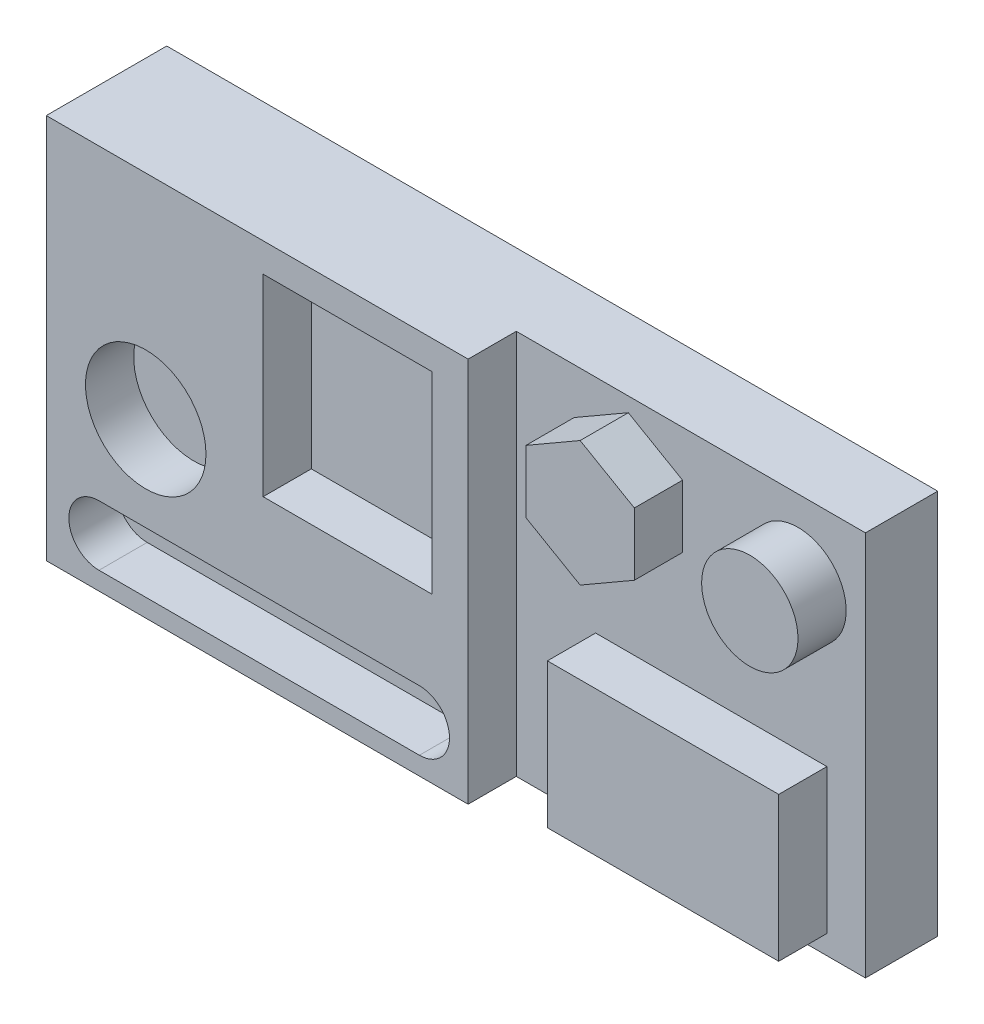
SolidWorks part; units mm, degrees
ref_plane "Front Plane" through (0, 0, 0) normal (0, 0, 1) x (1, 0, 0)
ref_plane "Top Plane" through (0, 0, 0) normal (0, 1, 0) x (1, 0, 0)
ref_plane "Right Plane" through (0, 0, 0) normal (1, 0, 0) x (0, 0, -1)
sketch "Sketch1" plane through (0, 0, 0) normal (0, 0, 1) x (1, 0, 0)
  line L0 (-87.7106, -38.1) -> (-3.262, -38.1) construction
  line L1 (-101.6, 50.8) -> (101.6, 50.8)
  line L2 (-101.6, 50.8) -> (-101.6, -50.8)
  line L3 (-101.6, -50.8) -> (101.6, -50.8)
  line L4 (101.6, 50.8) -> (101.6, -50.8)
  line L5 (-101.6, 50.8) -> (101.6, -50.8) construction
  line L6 (-101.6, -50.8) -> (101.6, 50.8) construction
  line L7 (-87.7106, -30.1625) -> (-3.262, -30.1625)
  line L8 (-87.7106, -46.0375) -> (-3.262, -46.0375)
  line L9 (9.5793, 50.8) -> (9.5793, -50.8)
  line L10 (-44.45, 43.18) -> (0, 43.18)
  line L11 (-44.45, 43.18) -> (-44.45, -7.62)
  line L12 (-44.45, -7.62) -> (0, -7.62)
  line L13 (0, 43.18) -> (0, -7.62)
  line L15 (30.48, -7.62) -> (91.44, -7.62)
  line L16 (30.48, -7.62) -> (30.48, -45.72)
  line L17 (30.48, -45.72) -> (91.44, -45.72)
  line L18 (91.44, -7.62) -> (91.44, -45.72)
  line L19 (39.1068, 13.9822) -> (53.3943, 22.2311)
  line L20 (53.3943, 22.2311) -> (53.3943, 38.7289)
  line L21 (53.3943, 38.7289) -> (39.1068, 46.9778)
  line L22 (39.1068, 46.9778) -> (24.8193, 38.7289)
  line L23 (24.8193, 38.7289) -> (24.8193, 22.2311)
  line L24 (24.8193, 22.2311) -> (39.1068, 13.9822)
  arc A0 (-87.7106, -30.1625) -> (-87.7106, -46.0375) centre (-87.7106, -38.1) ccw
  arc A1 (-3.262, -46.0375) -> (-3.262, -30.1625) centre (-3.262, -38.1) ccw
  circle A2 centre (-75.3876, -5.4366) radius 15.875
  circle A3 centre (83.82, 30.48) radius 12.7
  circle A4 centre (39.1068, 30.48) radius 14.2875 construction
  point P0 (0, 0)
  point P8 (-45.4863, -38.1)
  dimension "D5" = 31.75
  dimension "D10" = 25.4
  dimension "D1" = 101.6
  dimension "D2" = 203.2
  dimension "D3" = 15.875
  dimension "D4" = 12.7
  dimension "D6" = 57.15
  dimension "D7" = 44.45
  dimension "D8" = 7.62
  dimension "D9" = 50.8
  dimension "D11" = 60.96
  dimension "D12" = 38.1
  dimension "D13" = 5.08
  dimension "D14" = 17.78
  dimension "D15" = 20.32
  dimension "D16" = 15.24
  dimension "D17" = 28.575
sketch "Sketch2" plane through (0, 0, 0) normal (0, 0, 1) x (1, 0, 0)
  line L0 (-101.6, 50.8) -> (101.6, 50.8) construction
  line L1 (101.6, 50.8) -> (101.6, -50.8) construction
  line L2 (-101.6, -50.8) -> (101.6, -50.8) construction
  line L3 (-101.6, 50.8) -> (-101.6, -50.8) construction
  line L4 (-101.6, 50.8) -> (101.6, 50.8)
  line L5 (101.6, 50.8) -> (101.6, -50.8)
  line L6 (-101.6, -50.8) -> (101.6, -50.8)
  line L7 (-101.6, 50.8) -> (-101.6, -50.8)
extrude "Boss-Extrude1" add sketch "Sketch2" along normal blind 31.75
ref_plane "Plane1" through (0, 0, 31.75) normal (0, 0, 1) x (1, 0, 0)
sketch "Sketch3" plane through (0, 0, 31.75) normal (0, 0, 1) x (1, 0, 0)
  line L0 (9.5793, 50.8) -> (9.5793, -50.8) construction
  line L1 (-101.6, -50.8) -> (101.6, -50.8) construction
  line L2 (101.6, 50.8) -> (101.6, -50.8) construction
  line L3 (-101.6, 50.8) -> (101.6, 50.8) construction
  line L4 (9.5793, 50.8) -> (9.5793, -50.8)
  line L5 (9.5793, -50.8) -> (101.6, -50.8)
  line L6 (101.6, 50.8) -> (101.6, -50.8)
  line L7 (9.5793, 50.8) -> (101.6, 50.8)
extrude "Cut-Extrude1" cut sketch "Sketch3" against normal blind 12.7
ref_plane "Plane2" through (0, 0, 19.05) normal (0, 0, 1) x (1, 0, 0)
sketch "Sketch4" plane through (0, 0, 19.05) normal (0, 0, 1) x (1, 0, 0)
  line L0 (30.48, -7.62) -> (91.44, -7.62) construction
  line L1 (91.44, -7.62) -> (91.44, -45.72) construction
  line L2 (30.48, -45.72) -> (91.44, -45.72) construction
  line L3 (30.48, -7.62) -> (30.48, -45.72) construction
  line L4 (30.48, -7.62) -> (91.44, -7.62)
  line L5 (91.44, -7.62) -> (91.44, -45.72)
  line L6 (30.48, -45.72) -> (91.44, -45.72)
  line L7 (30.48, -7.62) -> (30.48, -45.72)
  circle A0 centre (83.82, 30.48) radius 12.7 construction
  circle A1 centre (83.82, 30.48) radius 12.7
extrude "Boss-Extrude2" add sketch "Sketch4" along normal blind 12.7
sketch "Sketch6" plane through (0, 0, 31.75) normal (0, 0, 1) x (1, 0, 0)
  line L0 (-87.7106, -30.1625) -> (-3.262, -30.1625) construction
  line L1 (-87.7106, -46.0375) -> (-3.262, -46.0375) construction
  line L2 (-44.45, -7.62) -> (0, -7.62) construction
  line L3 (0, 43.18) -> (0, -7.62) construction
  line L4 (-44.45, 43.18) -> (0, 43.18) construction
  line L5 (-44.45, 43.18) -> (-44.45, -7.62) construction
  line L6 (-87.7106, -30.1625) -> (-3.262, -30.1625)
  line L7 (-87.7106, -46.0375) -> (-3.262, -46.0375)
  line L8 (-44.45, -7.62) -> (0, -7.62)
  line L9 (0, 43.18) -> (0, -7.62)
  line L10 (-44.45, 43.18) -> (0, 43.18)
  line L11 (-44.45, 43.18) -> (-44.45, -7.62)
  arc A0 (-3.262, -46.0375) -> (-3.262, -30.1625) centre (-3.262, -38.1) ccw construction
  arc A1 (-87.7106, -30.1625) -> (-87.7106, -46.0375) centre (-87.7106, -38.1) ccw construction
  circle A2 centre (-75.3876, -5.4366) radius 15.875 construction
  arc A3 (-3.262, -46.0375) -> (-3.262, -30.1625) centre (-3.262, -38.1) ccw
  arc A4 (-87.7106, -30.1625) -> (-87.7106, -46.0375) centre (-87.7106, -38.1) ccw
  circle A5 centre (-75.3876, -5.4366) radius 15.875
extrude "Cut-Extrude2" cut sketch "Sketch6" against normal blind 12.7
sketch "Sketch7" plane through (0, 0, 19.05) normal (0, 0, 1) x (1, 0, 0)
  line L0 (39.1068, 46.9778) -> (24.8193, 38.7289) construction
  line L1 (24.8193, 38.7289) -> (24.8193, 22.2311) construction
  line L2 (24.8193, 22.2311) -> (39.1068, 13.9822) construction
  line L3 (39.1068, 13.9822) -> (53.3943, 22.2311) construction
  line L4 (53.3943, 22.2311) -> (53.3943, 38.7289) construction
  line L5 (53.3943, 38.7289) -> (39.1068, 46.9778) construction
  line L6 (39.1068, 46.9778) -> (24.8193, 38.7289)
  line L7 (24.8193, 38.7289) -> (24.8193, 22.2311)
  line L8 (24.8193, 22.2311) -> (39.1068, 13.9822)
  line L9 (39.1068, 13.9822) -> (53.3943, 22.2311)
  line L10 (53.3943, 22.2311) -> (53.3943, 38.7289)
  line L11 (53.3943, 38.7289) -> (39.1068, 46.9778)
extrude "Boss-Extrude3" add sketch "Sketch7" along normal blind 12.7
